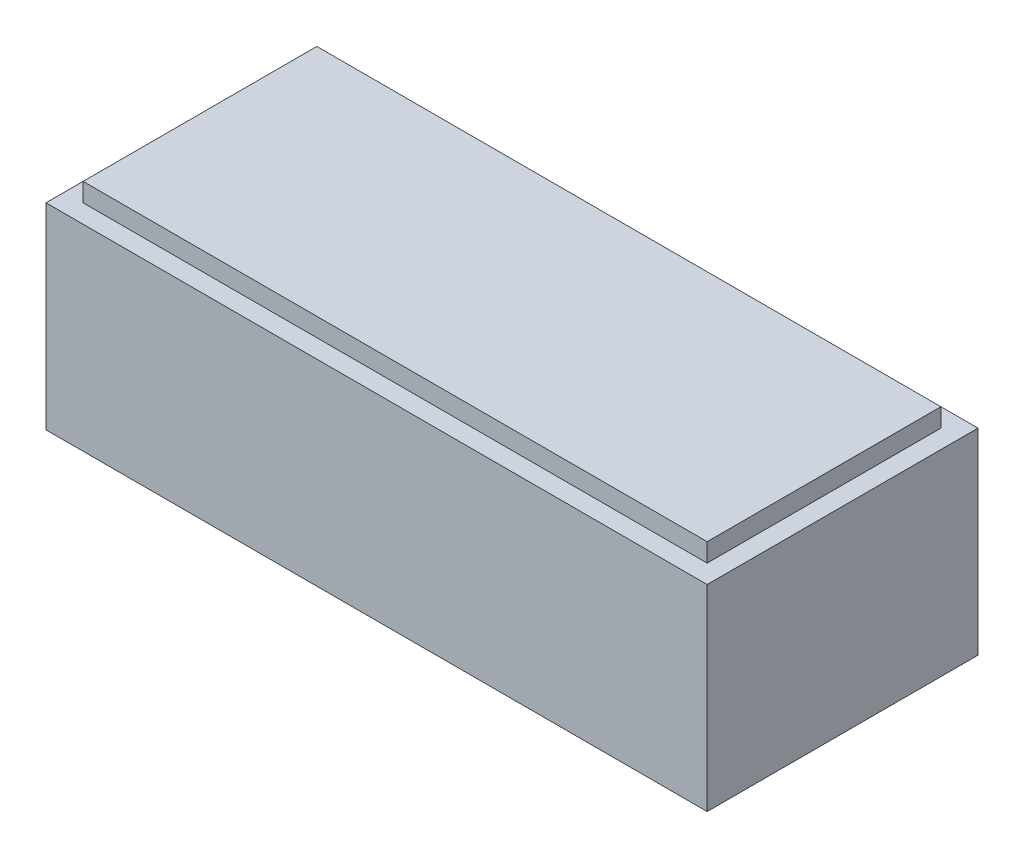
SolidWorks part; units mm, degrees
ref_plane "Front Plane" through (0, 0, 0) normal (0, 0, 1) x (1, 0, 0)
ref_plane "Top Plane" through (0, 0, 0) normal (0, 1, 0) x (1, 0, 0)
ref_plane "Right Plane" through (0, 0, 0) normal (1, 0, 0) x (0, 0, -1)
sketch "Sketch1" plane through (0, 0, 0) normal (0, 1, 0) x (1, 0, 0)
  line L1 (0, 0) -> (8.91, 0)
  line L2 (0, 0) -> (0, 3.65)
  line L3 (0, 3.65) -> (8.91, 3.65)
  line L4 (8.91, 0) -> (8.91, 3.65)
  dimension "D1" = 8.91
  dimension "D2" = 3.65
extrude "main shape" add sketch "Sketch1" along normal blind 2.65
sketch "Sketch2" plane through (0, 2.65, 0) normal (0, 1, 0) x (1, 0, 0)
  line L0 (8.91, 3.65) -> (0, 3.65) construction
  line L1 (0.25, 0.25) -> (8.66, 0.25)
  line L2 (0.25, 0.25) -> (0.25, 3.4)
  line L3 (0.25, 3.4) -> (8.66, 3.4)
  line L4 (8.66, 0.25) -> (8.66, 3.4)
  line L5 (0, 3.65) -> (0, 0) construction
  line L6 (8.91, 0) -> (8.91, 3.65) construction
  line L7 (0, 0) -> (8.91, 0) construction
  dimension "D1" = 0.25
  dimension "D2" = 0.25
  dimension "D3" = 0.25
  dimension "D4" = 0.25
extrude "bottom base" add sketch "Sketch2" along normal blind 0.25
sketch "switch hole" plane through (0, 0, 0) normal (0, -1, 0) x (1, 0, 0)
  line L0 (8.91, -1.825) -> (6.41, -1.825)
  line L1 (8.91, 0) -> (8.91, -3.65) construction
  line L2 (0, -1.825) -> (2.5, -1.825)
  line L5 (2.5, -0.975) -> (6.41, -0.975)
  line L6 (2.5, -0.975) -> (2.5, -2.675)
  line L7 (2.5, -2.675) -> (6.41, -2.675)
  line L8 (6.41, -0.975) -> (6.41, -2.675)
  line L10 (0, -3.65) -> (0, 0) construction
  point P13 (2.5, -1.825)
  dimension "D1" = 2.5
  dimension "D2" = 2.5
  dimension "D3" = 1.7
extrude "Cut-Extrude1" cut sketch "switch hole" against normal blind 0.5 contours L8 L5 L6 L7
